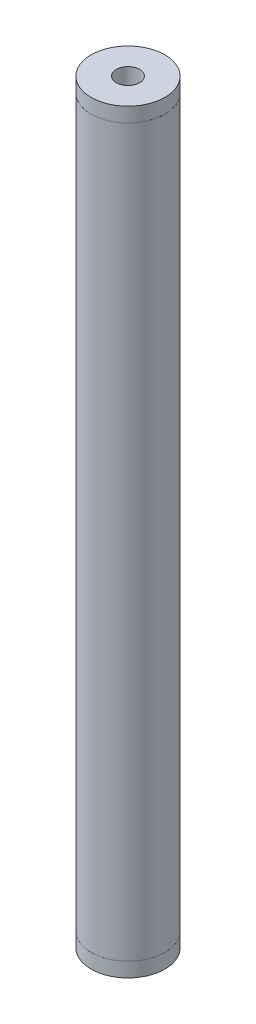
SolidWorks part; units mm, degrees
ref_plane "Plano frontal" through (0, 0, 0) normal (0, 0, 1) x (1, 0, 0)
ref_plane "Plano superior" through (0, 0, 0) normal (0, 1, 0) x (1, 0, 0)
ref_plane "Plano direito" through (0, 0, 0) normal (1, 0, 0) x (0, 0, -1)
sketch "Esboço1" plane through (0, 0, 0) normal (0, 1, 0) x (1, 0, 0)
  circle A0 centre (0, 0) radius 25.4
  circle A1 centre (0, 0) radius 21.65
  dimension "D1" = 50.8
  dimension "D2" = 3.75
extrude "Ressalto-extrusão1" add sketch "Esboço1" along normal blind 500
sketch "Esboço2" plane through (0, 0, 0) normal (0, 0, 1) x (1, 0, 0)
  line L0 (25.4, 500) -> (25.4, 510)
  line L1 (25.4, 510) -> (8, 510)
  line L2 (25.4, 250) -> (-25.4, 250) construction
  line L3 (8, 460) -> (21.65, 460)
  line L4 (21.65, 0) -> (21.65, 500) construction
  line L5 (21.65, 460) -> (21.65, 500)
  line L6 (21.65, 500) -> (25.4, 500)
  line L7 (0, 0) -> (0, 1267.5742) construction
  line L8 (8, 510) -> (8, 460)
  line L9 (25.4, 0) -> (25.4, 500) construction
  line L10 (-25.4, 500) -> (-25.4, 0) construction
  line L11 (8, -10) -> (8, 40)
  line L12 (21.65, 0) -> (25.4, 0)
  line L13 (21.65, 40) -> (21.65, 0)
  line L14 (8, 40) -> (21.65, 40)
  line L15 (25.4, -10) -> (8, -10)
  line L16 (25.4, 0) -> (25.4, -10)
  dimension "D1" = 16
  dimension "D2" = 10
  dimension "D3" = 50
revolve "Revolução1" add sketch "Esboço2" angle 360 about L7
